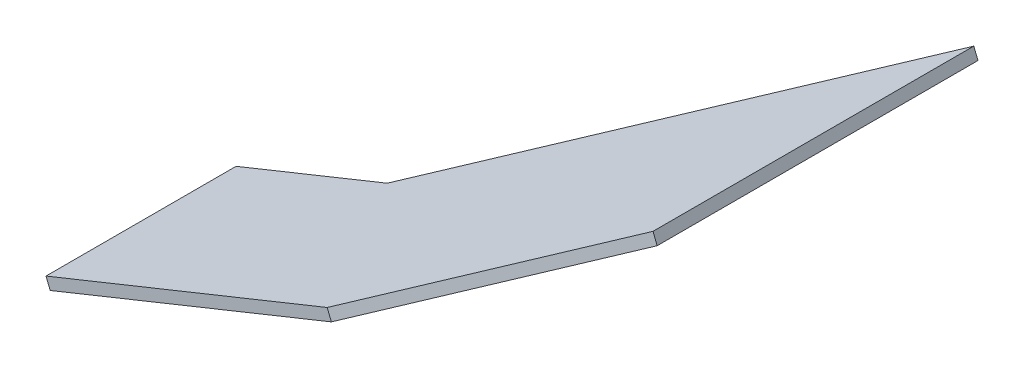
SolidWorks part; units mm, degrees
ref_plane "Front Plane" through (0, 0, 0) normal (0, 0, 1) x (1, 0, 0)
ref_plane "Top Plane" through (0, 0, 0) normal (0, 1, 0) x (1, 0, 0)
ref_plane "Right Plane" through (0, 0, 0) normal (1, 0, 0) x (0, 0, -1)
ref_plane "Plane1" through (-347.9973, 863.1162, 0) normal (0.3739, -0.9275, 0) x (0.9275, 0.3739, 0)
sketch "Sketch2" plane through (-347.9973, 863.1162, 0) normal (0.3739, -0.9275, 0) x (0.9275, 0.3739, 0)
  line L0 (6688.4765, -11775.449) -> (6688.4765, -11826.3106)
  line L2 (6688.4765, -11826.3106) -> (6732.0858, -11826.3106)
  line L4 (6732.0858, -11826.3106) -> (6816.4765, -11905.0061)
  line L5 (6816.4765, -11905.0061) -> (6816.4765, -11819.1568)
  line L6 (6816.4765, -11819.1568) -> (6769.6056, -11775.449)
  line L8 (6769.6056, -11775.449) -> (6688.4765, -11775.449)
  dimension "D1" = 6769.6056
  dimension "D2" = 11775.449
  dimension "D3" = 6688.4765
  dimension "D4" = 6732.0858
  dimension "D5" = 6816.4765
  dimension "D6" = 11819.1568
  dimension "D7" = 11826.3106
extrude "Boss-Extrude1" add sketch "Sketch2" along normal blind 3
